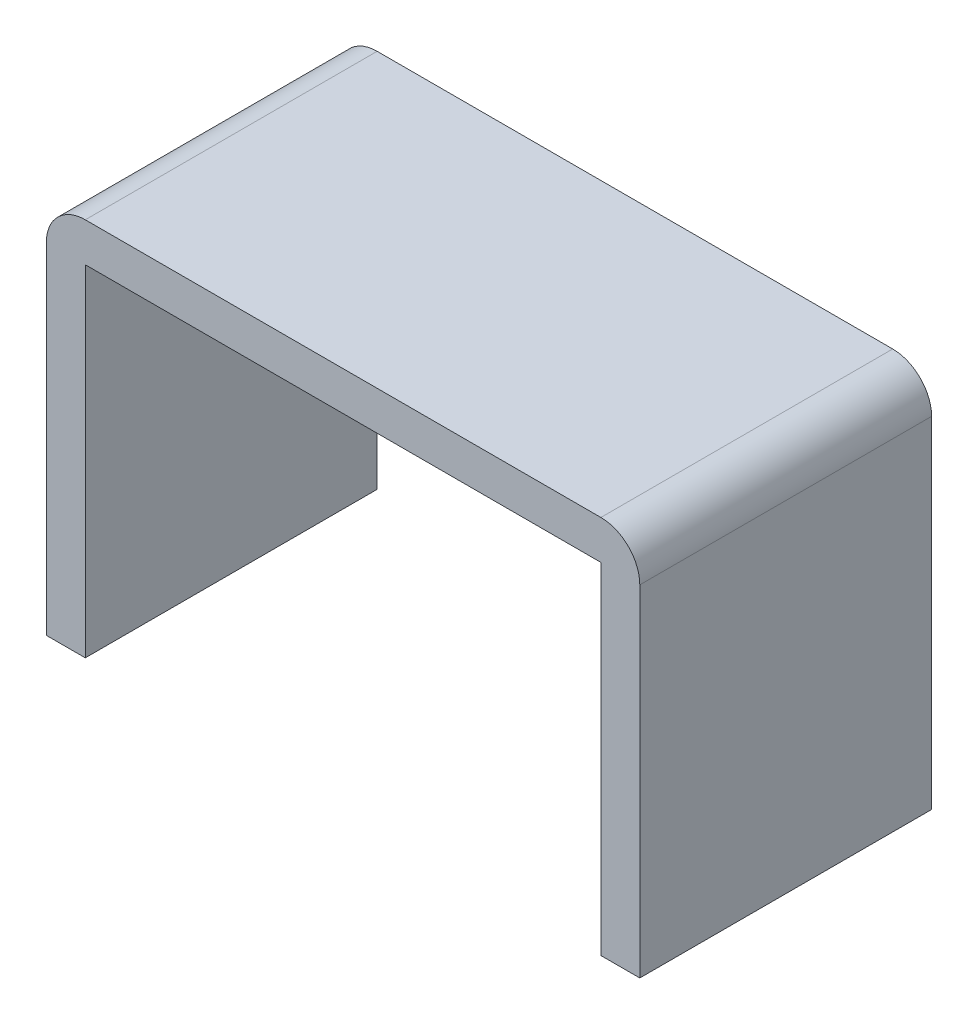
SolidWorks part; units mm, degrees
ref_plane "Front Plane" through (0, 0, 0) normal (0, 0, 1) x (1, 0, 0)
ref_plane "Top Plane" through (0, 0, 0) normal (0, 1, 0) x (1, 0, 0)
ref_plane "Right Plane" through (0, 0, 0) normal (1, 0, 0) x (0, 0, -1)
sketch "Sketch1" plane through (0, 0, 0) normal (0, 0, 1) x (1, 0, 0)
  line L0 (0, 0) -> (0, 35)
  line L1 (4, 39) -> (57, 39)
  line L2 (61, 35) -> (61, 0)
  line L3 (61, 0) -> (57, 0)
  line L4 (57, 0) -> (57, 35)
  line L5 (57, 35) -> (4, 35)
  line L6 (4, 35) -> (4, 0)
  line L7 (4, 0) -> (0, 0)
  arc A0 (57, 39) -> (61, 35) centre (57, 35) cw
  arc A1 (0, 35) -> (4, 39) centre (4, 35) cw
  dimension "D6" = 4
  dimension "D1" = 53
  dimension "D2" = 4
  dimension "D3" = 4
  dimension "D4" = 4
  dimension "D5" = 35
extrude "Boss-Extrude1" add sketch "Sketch1" along normal blind 30
